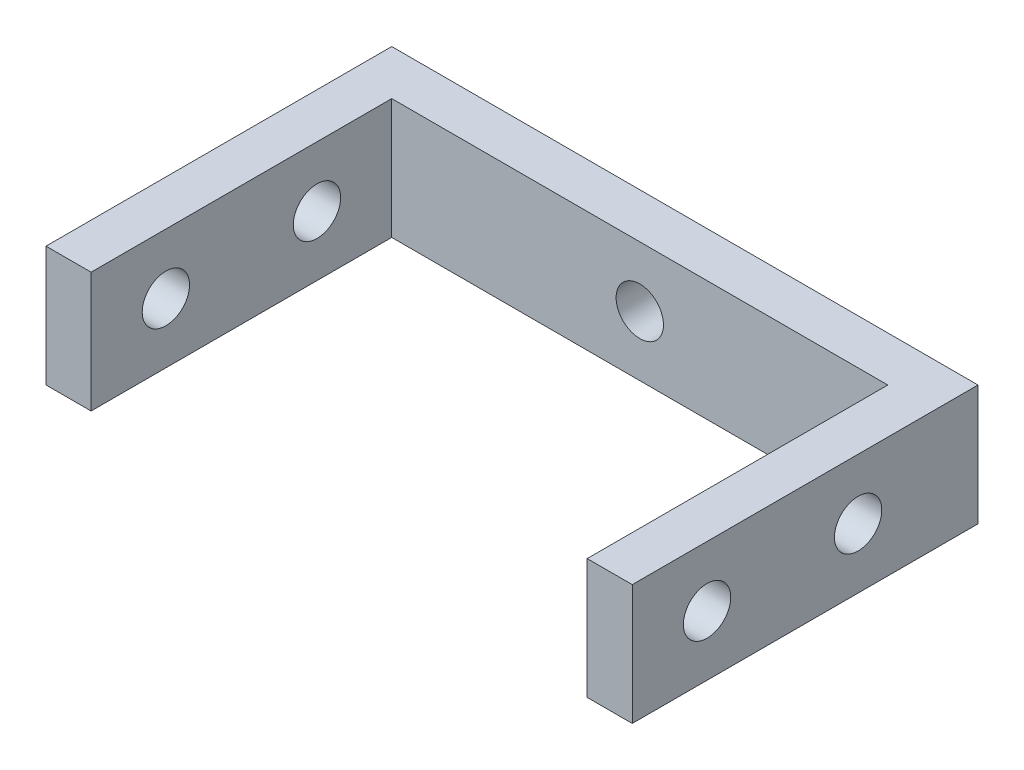
SolidWorks part; units mm, degrees
ref_plane "Front Plane" through (0, 0, 0) normal (0, 0, 1) x (1, 0, 0)
ref_plane "Top Plane" through (0, 0, 0) normal (0, 1, 0) x (1, 0, 0)
ref_plane "Right Plane" through (0, 0, 0) normal (1, 0, 0) x (0, 0, -1)
sketch "Sketch1" plane through (0, 0, 0) normal (0, 0, 1) x (1, 0, 0)
  line L1 (-19.5, -4) -> (19.5, -4)
  line L2 (-19.5, -4) -> (-19.5, 4)
  line L3 (-19.5, 4) -> (19.5, 4)
  line L4 (19.5, -4) -> (19.5, 4)
  line L5 (-19.5, -4) -> (19.5, 4) construction
  line L6 (-19.5, 4) -> (19.5, -4) construction
  point P0 (0, 0)
  dimension "D1" = 39
  dimension "D2" = 8
extrude "Boss-Extrude1" add sketch "Sketch1" along normal blind 3
sketch "Sketch2" plane through (0, 0, 3) normal (0, 0, 1) x (1, 0, 0)
  line L0 (-19.5, -4) -> (19.5, -4) construction
  line L1 (-19.5, 4) -> (-16.5, 4)
  line L2 (-19.5, 4) -> (-19.5, -4)
  line L3 (-19.5, -4) -> (-16.5, -4)
  line L4 (-16.5, 4) -> (-16.5, -4)
  line L6 (19.5, 4) -> (16.5, 4)
  line L7 (19.5, 4) -> (19.5, -4)
  line L8 (19.5, -4) -> (16.5, -4)
  line L9 (16.5, 4) -> (16.5, -4)
  dimension "D1" = 3
  dimension "D2" = 3
extrude "Boss-Extrude2" add sketch "Sketch2" along normal blind 20
sketch "Sketch3" plane through (-19.5, 0, 0) normal (-1, 0, 0) x (0, 0, 1)
  line L0 (23, 4) -> (23, -4) construction
  line L1 (0, 4) -> (0, -4) construction
  circle A0 centre (18.025, 0) radius 1.575
  circle A1 centre (7.975, 0) radius 1.575
  dimension "D1" = 3.15
  dimension "D2" = 3.15
  dimension "D3" = 4.975
  dimension "D4" = 7.975
extrude "Cut-Extrude1" cut sketch "Sketch3" against normal through all
sketch "Sketch4" plane through (0, 0, 3) normal (0, 0, 1) x (1, 0, 0)
  circle A0 centre (0, 0) radius 1.575
  dimension "D1" = 3.15
extrude "Cut-Extrude2" cut sketch "Sketch4" against normal blind 3
